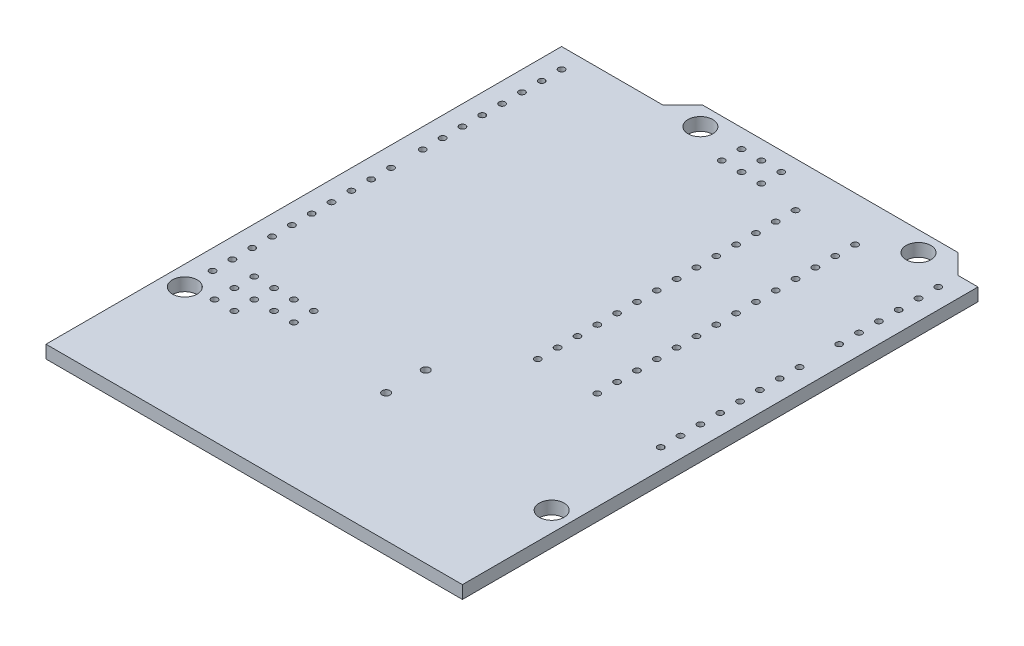
SolidWorks part; units mm, degrees
material "E-Glass Fiber"
ref_plane "Front Plane" through (0, 0, 0) normal (0, 0, 1) x (1, 0, 0)
ref_plane "Top Plane" through (0, 0, 0) normal (0, 1, 0) x (1, 0, 0)
ref_plane "Right Plane" through (0, 0, 0) normal (1, 0, 0) x (0, 0, -1)
sketch "Sketch1" plane through (0, 0, 0) normal (0, 1, 0) x (1, 0, 0)
  line L0 (-29.337, 0) -> (29.337, 0) construction
  line L1 (0, 0) -> (-53.34, 0)
  line L2 (0, 0) -> (0, 66.04)
  line L3 (-5.08, 68.58) -> (-37.846, 68.58)
  line L4 (-53.34, 0) -> (-53.34, 66.04)
  line L5 (-53.34, 66.04) -> (-40.386, 66.04)
  line L6 (-40.386, 66.04) -> (-37.846, 68.58)
  line L7 (-5.08, 68.58) -> (-2.54, 66.04)
  line L8 (-2.54, 66.04) -> (0, 66.04)
  circle A0 centre (-7.62, 66.04) radius 1.5875
  circle A1 centre (-35.56, 66.04) radius 1.5875
  circle A2 centre (-2.54, 13.97) radius 1.5875
  circle A3 centre (-50.8, 15.24) radius 1.5875
  dimension "D8" = 3.175
  dimension "D1" = 68.58
  dimension "D2" = 53.34
  dimension "D3" = 66.04
  dimension "D4" = 2.54
  dimension "D5" = 45
  dimension "D6" = 45
  dimension "D7" = 40.386
  dimension "D9" = 66.04
  dimension "D10" = 35.56
  dimension "D11" = 7.62
  dimension "D12" = 13.97
  dimension "D13" = 2.54
  dimension "D14" = 15.24
  dimension "D15" = 50.8
extrude "Boss-Extrude1" add sketch "Sketch1" against normal blind 1.65
sketch "Sketch2" plane through (0, 0, 0) normal (0, 1, 0) x (1, 0, 0)
  line L0 (0, -0.9075) -> (0, 0.9075) construction
  line L1 (-0.9075, 0) -> (0.9075, 0) construction
  circle A0 centre (-2.54, 27.94) radius 0.4
  dimension "D1" = 0.8
  dimension "D2" = 2.54
  dimension "D3" = 27.94
extrude "Cut-Extrude1" cut sketch "Sketch2" against normal blind 1.65
sketch "Sketch3" plane through (0, 0, 0) normal (0, 1, 0) x (1, 0, 0)
  line L0 (0, -0.9075) -> (0, 0.9075) construction
  line L1 (-0.9075, 0) -> (0.9075, 0) construction
  circle A0 centre (-50.8, 18.796) radius 0.4
  dimension "D2" = 0.8
  dimension "D1" = 50.8
  dimension "D3" = 18.796
extrude "Cut-Extrude2" cut sketch "Sketch3" against normal blind 1.65
pattern_linear "LPattern1" count 15 spacing 2.54 along (0, 0, -1) skipping (8, 0) of "Cut-Extrude1"
sketch "Sketch4" plane through (0, 0, 0) normal (0, 1, 0) x (1, 0, 0)
  line L0 (-0.9075, 0) -> (0.9075, 0) construction
  line L1 (0, -0.9075) -> (0, 0.9075) construction
  circle A0 centre (-50.8, 45.72) radius 0.4
  dimension "D3" = 0.8
  dimension "D1" = 45.72
  dimension "D2" = 50.8
extrude "Cut-Extrude3" cut sketch "Sketch4" against normal blind 1.65
pattern_linear "LPattern2" count 10 spacing 2.54 along (0, 0, -1) of "Cut-Extrude2"
pattern_linear "LPattern3" count 8 spacing 2.54 along (0, 0, -1) of "Cut-Extrude3"
sketch "Sketch5" plane through (0, 0, 0) normal (0, 1, 0) x (1, 0, 0)
  line L0 (-27.89, 66.18) -> (-27.89, 63.64) construction
  line L1 (-30.43, 66.18) -> (-25.35, 66.18) construction
  line L2 (-30.43, 66.18) -> (-30.43, 63.64) construction
  line L3 (-30.43, 63.64) -> (-25.35, 63.64) construction
  line L4 (-25.35, 66.18) -> (-25.35, 63.64) construction
  line L5 (-0.9075, 0) -> (0.9075, 0) construction
  line L6 (0, -0.9075) -> (0, 0.9075) construction
  circle A0 centre (-30.43, 66.18) radius 0.4
  circle A1 centre (-27.89, 66.18) radius 0.4
  circle A2 centre (-25.35, 66.18) radius 0.4
  circle A3 centre (-25.35, 63.64) radius 0.4
  circle A4 centre (-27.89, 63.64) radius 0.4
  circle A5 centre (-30.43, 63.64) radius 0.4
  circle A6 centre (-47.498, 15.748) radius 0.4
  circle A7 centre (-47.498, 18.288) radius 0.4
  circle A8 centre (-47.498, 20.828) radius 0.4
  circle A9 centre (-44.958, 20.828) radius 0.4
  circle A10 centre (-44.958, 18.288) radius 0.4
  circle A11 centre (-44.958, 15.748) radius 0.4
  circle A12 centre (-42.418, 18.288) radius 0.4
  circle A13 centre (-42.418, 20.828) radius 0.4
  circle A14 centre (-39.878, 20.828) radius 0.4
  circle A15 centre (-39.878, 18.288) radius 0.4
  circle A16 centre (-26.162, 21.463) radius 0.5
  circle A17 centre (-26.162, 16.383) radius 0.5
  dimension "D4" = 0.8
  dimension "D14" = 1
  dimension "D1" = 2.54
  dimension "D2" = 2.54
  dimension "D3" = 2.54
  dimension "D5" = 63.64
  dimension "D6" = 30.43
  dimension "D7" = 2.54
  dimension "D8" = 2.54
  dimension "D9" = 2.54
  dimension "D10" = 2.54
  dimension "D11" = 2.54
  dimension "D12" = 47.498
  dimension "D13" = 15.748
  dimension "D15" = 5.08
  dimension "D16" = 16.383
  dimension "D17" = 26.162
extrude "Cut-Extrude4" cut sketch "Sketch5" against normal blind 10
sketch "Sketch6" plane through (0, 0, 0) normal (0, 1, 0) x (1, 0, 0)
  line L0 (0, -0.9075) -> (0, 0.9075) construction
  line L1 (-0.9075, 0) -> (0.9075, 0) construction
  line L2 (-20.193, 29.845) -> (-20.193, 32.385) construction
  circle A0 centre (-20.193, 29.845) radius 0.4
  circle A1 centre (-12.573, 29.845) radius 0.4
  circle A2 centre (-20.193, 32.385) radius 0.4
  circle A3 centre (-12.573, 32.385) radius 0.4
  circle A4 centre (-20.193, 34.925) radius 0.4
  circle A5 centre (-12.573, 34.925) radius 0.4
  circle A6 centre (-20.193, 37.465) radius 0.4
  circle A7 centre (-12.573, 37.465) radius 0.4
  circle A8 centre (-20.193, 40.005) radius 0.4
  circle A9 centre (-12.573, 40.005) radius 0.4
  circle A10 centre (-20.193, 42.545) radius 0.4
  circle A11 centre (-12.573, 42.545) radius 0.4
  circle A12 centre (-20.193, 45.085) radius 0.4
  circle A13 centre (-12.573, 45.085) radius 0.4
  circle A14 centre (-20.193, 47.625) radius 0.4
  circle A15 centre (-12.573, 47.625) radius 0.4
  circle A16 centre (-20.193, 50.165) radius 0.4
  circle A17 centre (-12.573, 50.165) radius 0.4
  circle A18 centre (-20.193, 52.705) radius 0.4
  circle A19 centre (-12.573, 52.705) radius 0.4
  circle A20 centre (-20.193, 55.245) radius 0.4
  circle A21 centre (-12.573, 55.245) radius 0.4
  circle A22 centre (-20.193, 57.785) radius 0.4
  circle A23 centre (-12.573, 57.785) radius 0.4
  circle A24 centre (-20.193, 60.325) radius 0.4
  circle A25 centre (-12.573, 60.325) radius 0.4
  circle A26 centre (-20.193, 62.865) radius 0.4
  circle A27 centre (-12.573, 62.865) radius 0.4
  dimension "D1" = 0.8
  dimension "D2" = 7.62
  dimension "D3" = 12.573
  dimension "D4" = 29.845
  dimension "D6" = 2.54
  dimension "D5" = 14
extrude "Cut-Extrude5" cut sketch "Sketch6" against normal blind 10
equation "\"D13@Sketch5\"=0.001*25.4*620"
equation "\"D16@Sketch5\"=645*0.001*25.4"
